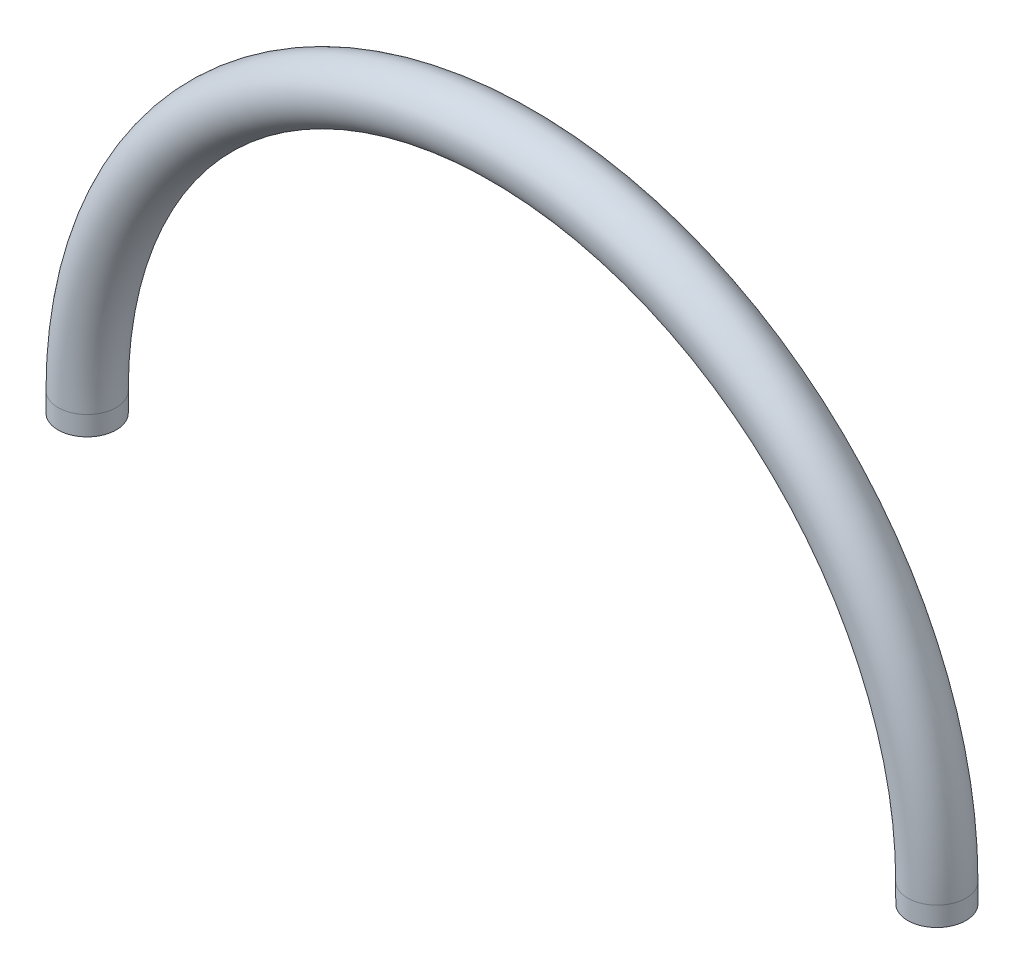
SolidWorks part; units mm, degrees
ref_plane "Front Plane" through (0, 0, 0) normal (0, 0, 1) x (1, 0, 0)
ref_plane "Top Plane" through (0, 0, 0) normal (0, 1, 0) x (1, 0, 0)
ref_plane "Right Plane" through (0, 0, 0) normal (1, 0, 0) x (0, 0, -1)
sketch "Sketch2" plane through (0, 0, 0) normal (0, 0, 1) x (1, 0, 0)
  line L0 (0, 42.9196) -> (0, -45.7432) construction
  line L1 (-55.626, 0) -> (-55.626, -2.54)
  line L2 (55.626, 0) -> (55.626, -2.54)
  arc A0 (-55.626, 0) -> (55.626, 0) centre (0, 0) cw
  dimension "D1" = 111.252
  dimension "D2" = 2.54
sweep "Sweep1" add path "Sketch2" circular profile diameter 7.62 parameters "D3"=7.62
